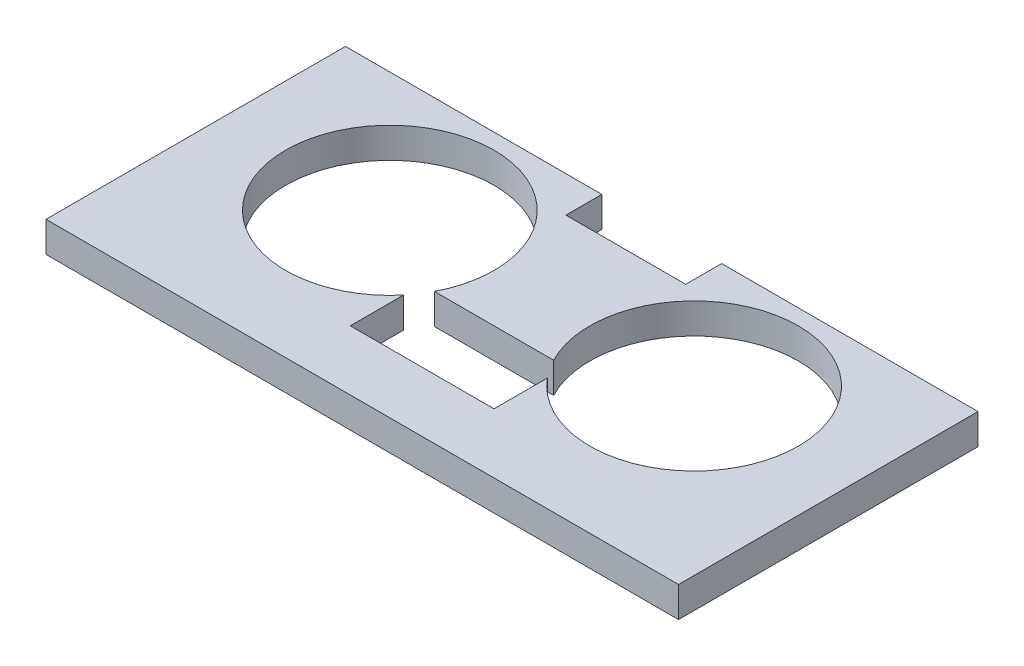
SolidWorks part; units mm, degrees
ref_plane "Front Plane" through (0, 0, 0) normal (0, 0, 1) x (1, 0, 0)
ref_plane "Top Plane" through (0, 0, 0) normal (0, 1, 0) x (1, 0, 0)
ref_plane "Right Plane" through (0, 0, 0) normal (1, 0, 0) x (0, 0, -1)
sketch "Sketch1" plane through (0, 0, 0) normal (0, 1, 0) x (1, 0, 0)
  line L0 (-29.3333, -8.5) -> (50.6667, -8.5) construction
  line L1 (-20.8, 11.5) -> (32, 11.5)
  line L2 (-20.8, 11.5) -> (-20.8, -13.5)
  line L3 (-20.8, -13.5) -> (32, -13.5)
  line L4 (32, 11.5) -> (32, -13.5)
  line L6 (-0.4, -8.5) -> (11.6, -8.5)
  line L7 (-0.4, -8.5) -> (-0.4, -2.5)
  line L8 (-0.4, -2.5) -> (11.6, -2.5)
  line L9 (11.6, -8.5) -> (11.6, -2.5)
  line L10 (0.6, 11.5) -> (10.6, 11.5)
  line L11 (0.6, 11.5) -> (0.6, 8.5)
  line L12 (0.6, 8.5) -> (10.6, 8.5)
  line L13 (10.6, 11.5) -> (10.6, 8.5)
  circle A0 centre (-7.1, 1.5) radius 8.7
  circle A1 centre (18.3, 1.5) radius 8.7
  dimension "D10" = 17.4
  dimension "D12" = 17.4
  dimension "D1" = 25
  dimension "D2" = 52.8
  dimension "D3" = 5
  dimension "D4" = 10
  dimension "D5" = 12
  dimension "D6" = 3
  dimension "D7" = 6
  dimension "D8" = 20.4
  dimension "D9" = 21.4
  dimension "D11" = 10
  dimension "D13" = 10
  dimension "D14" = 13.7
  dimension "D15" = 25.4
extrude "Boss-Extrude1" add sketch "Sketch1" along normal blind 2.54 contours L2 L0 L7 A0 L8 A1 L9 L4 L1 L13 L12 L11 | L0 L2 L3 L4 L6
